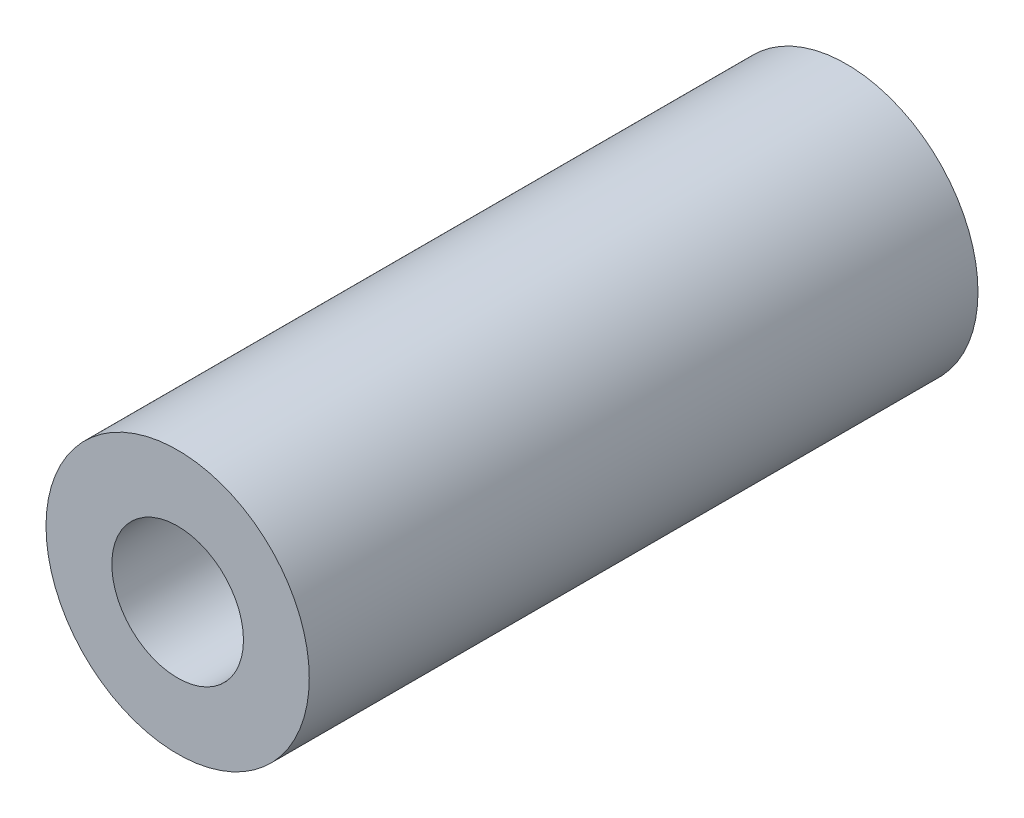
SolidWorks part; units mm, degrees
material "PVC Rigid"
ref_plane "Front Plane" through (0, 0, 0) normal (0, 0, 1) x (1, 0, 0)
ref_plane "Top Plane" through (0, 0, 0) normal (0, 1, 0) x (1, 0, 0)
ref_plane "Right Plane" through (0, 0, 0) normal (1, 0, 0) x (0, 0, -1)
sketch "Sketch1" plane through (0, 0, 0) normal (0, 0, 1) x (1, 0, 0)
  circle A0 centre (0, 0) radius 3.175
  circle A1 centre (0, 0) radius 6.35
  dimension "D1" = 6.35
  dimension "D2" = 12.7
extrude "Boss-Extrude1" add sketch "Sketch1" along normal blind 32.258
